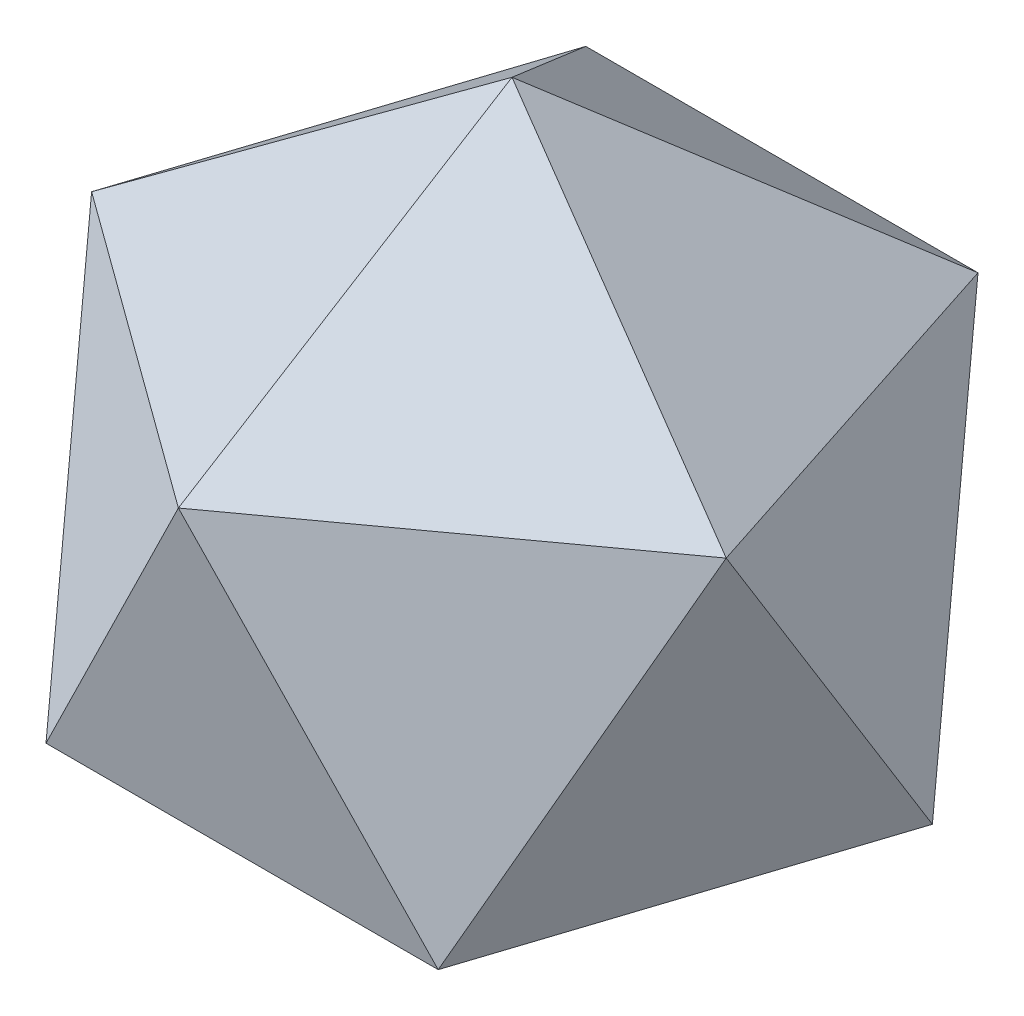
SolidWorks part; units mm, degrees
ref_plane "Front Plane" through (0, 0, 0) normal (0, 0, 1) x (1, 0, 0)
ref_plane "Top Plane" through (0, 0, 0) normal (0, 1, 0) x (1, 0, 0)
ref_plane "Right Plane" through (0, 0, 0) normal (1, 0, 0) x (0, 0, -1)
sketch3d "3DSketch2"
  line L0 (0, 0, 0) -> (0, 0, -22.3607) construction
  line L1 (0, 0, -22.3607) -> (-21.2663, 0, -6.9098) construction
  line L2 (-21.2663, 0, -6.9098) -> (-13.1433, 0, 18.0902) construction
  line L3 (-13.1433, 0, 18.0902) -> (13.1433, 0, 18.0902) construction
  line L4 (13.1433, 0, 18.0902) -> (21.2663, 0, -6.9098) construction
  line L5 (21.2663, 0, -6.9098) -> (0, 0, -22.3607)
  line L6 (0, 0, 0) -> (21.2663, 0, -6.9098) construction
  line L7 (0, 0, 0) -> (-13.1433, 0, 18.0902) construction
  line L8 (0, 0, 0) -> (-21.2663, 0, -6.9098) construction
  line L9 (0, 0, 0) -> (13.1433, 0, 18.0902) construction
  line L10 (0, 36.1803, 0) -> (0, -13.8197, 0) construction
  line L11 (21.2663, 0, -6.9098) -> (0, -13.8197, 0)
  line L12 (0, -13.8197, 0) -> (13.1433, 0, 18.0902) construction
  line L13 (-13.1433, 0, 18.0902) -> (0, -13.8197, 0) construction
  line L14 (-21.2663, 0, -6.9098) -> (0, -13.8197, 0) construction
  line L15 (0, 0, -22.3607) -> (0, -13.8197, 0)
  line L16 (0, 22.3607, 0) -> (-10.6331, 22.3607, -14.6353) construction
  line L17 (-10.6331, 22.3607, -14.6353) -> (-10.6331, 0, -14.6353) construction
  line L18 (-10.6331, 22.3607, -14.6353) -> (-13.1433, 22.3607, -18.0902) construction
  line L19 (-13.1433, 22.3607, -18.0902) -> (-21.2663, 22.3607, 6.9098) construction
  line L20 (-21.2663, 22.3607, 6.9098) -> (0, 22.3607, 22.3607) construction
  line L21 (0, 22.3607, 22.3607) -> (21.2663, 22.3607, 6.9098) construction
  line L22 (21.2663, 22.3607, 6.9098) -> (13.1433, 22.3607, -18.0902)
  line L23 (13.1433, 22.3607, -18.0902) -> (-13.1433, 22.3607, -18.0902) construction
  line L24 (-21.2663, 22.3607, 6.9098) -> (0, 22.3607, 0) construction
  line L25 (21.2663, 22.3607, 6.9098) -> (0, 22.3607, 0) construction
  line L26 (0, 22.3607, 0) -> (0, 22.3607, 22.3607) construction
  line L27 (0, 22.3607, 0) -> (13.1433, 22.3607, -18.0902) construction
  line L28 (0, 36.1803, 0) -> (0, 22.3607, 22.3607) construction
  line L29 (0, 36.1803, 0) -> (21.2663, 22.3607, 6.9098)
  line L30 (13.1433, 22.3607, -18.0902) -> (0, 0, -22.3607)
  line L31 (13.1433, 22.3607, -18.0902) -> (21.2663, 0, -6.9098)
  line L32 (21.2663, 22.3607, 6.9098) -> (21.2663, 0, -6.9098)
  line L33 (0, 36.1803, 0) -> (13.1433, 22.3607, -18.0902)
  dimension "D1" = 50
ref_plane "Plane1" through (3.9186, -8.7268, -5.3934) normal (0.3568, -0.7947, -0.4911) x (-0.9342, -0.3035, -0.1876)
sketch "Sketch2" plane through (3.9186, -8.7268, -5.3934) normal (0.3568, -0.7947, -0.4911) x (-0.9342, -0.3035, -0.1876)
  line L0 (4.1947, 19.0211) -> (4.1947, -7.2654) construction
  line L1 (-18.5701, 5.8779) -> (4.1947, -7.2654) construction
  line L2 (-18.5701, 5.8779) -> (4.1947, 19.0211) construction
  line L3 (4.1947, 19.0211) -> (4.1947, -7.2654)
  line L4 (-18.5701, 5.8779) -> (4.1947, -7.2654)
  line L5 (-18.5701, 5.8779) -> (4.1947, 19.0211)
surface "Surface-Fill1" sketch "Sketch2"
ref_plane "Plane2" through (10.2589, -3.3333, -14.1202) normal (-0.5774, 0.1876, 0.7947) x (0.8165, 0.1326, 0.5619)
sketch "Sketch3" plane through (10.2589, -3.3333, -14.1202) normal (-0.5774, 0.1876, 0.7947) x (0.8165, 0.1326, 0.5619)
  line L0 (3.5326, 25.9188) -> (13.4812, 1.5876) construction
  line L1 (13.4812, 1.5876) -> (-12.5646, 5.1374) construction
  line L2 (3.5326, 25.9188) -> (-12.5646, 5.1374) construction
  line L3 (3.5326, 25.9188) -> (13.4812, 1.5876)
  line L4 (13.4812, 1.5876) -> (-12.5646, 5.1374)
  line L5 (3.5326, 25.9188) -> (-12.5646, 5.1374)
surface "Surface-Fill2" sketch "Sketch3"
ref_plane "Plane5" through (20.5179, 4.1202, -6.6667) normal (-0.9342, -0.1876, 0.3035) x (0.2976, 0.0598, 0.9528)
sketch "Sketch5" plane through (20.5179, 4.1202, -6.6667) normal (-0.9342, -0.1876, 0.3035) x (0.2976, 0.0598, 0.9528)
  line L0 (-11.9891, 19.3354) -> (-0.2552, -4.1869) construction
  line L1 (14.2487, 17.7361) -> (-0.2552, -4.1869) construction
  line L2 (14.2487, 17.7361) -> (-11.9891, 19.3354) construction
  line L3 (-11.9891, 19.3354) -> (-0.2552, -4.1869)
  line L4 (14.2487, 17.7361) -> (-0.2552, -4.1869)
  line L5 (14.2487, 17.7361) -> (-11.9891, 19.3354)
surface "Surface-Fill3" sketch "Sketch5"
ref_plane "Plane6" through (16.5993, 22.847, -5.3934) normal (0.5774, 0.7947, -0.1876) x (0.8165, -0.5619, 0.1326)
sketch "Sketch6" plane through (16.5993, 22.847, -5.3934) normal (0.5774, 0.7947, -0.1876) x (0.8165, -0.5619, 0.1326)
  line L0 (5.7158, -11.8624) -> (-4.2328, 12.4688) construction
  line L1 (-20.3299, -8.3125) -> (5.7158, -11.8624) construction
  line L2 (-20.3299, -8.3125) -> (-4.2328, 12.4688) construction
  line L3 (5.7158, -11.8624) -> (-4.2328, 12.4688)
  line L4 (-20.3299, -8.3125) -> (5.7158, -11.8624)
  line L5 (-20.3299, -8.3125) -> (-4.2328, 12.4688)
surface "Surface-Fill4" sketch "Sketch6"
pattern_circular "CirPattern1" count 5 over 360 about axis through (0, 0, 0) along (0, 1, 0)
surface "Surface-Knit1"
